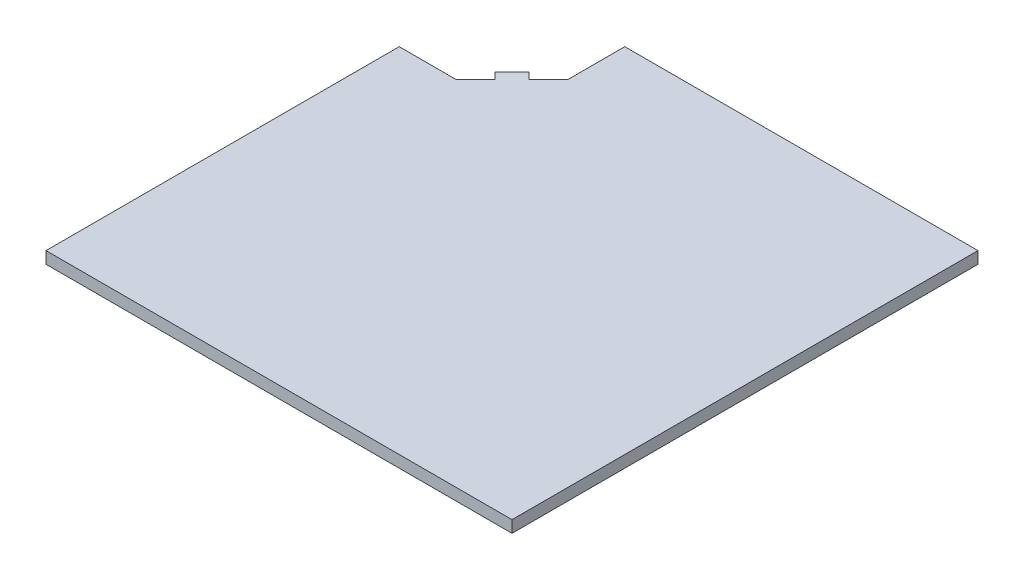
SolidWorks part; units mm, degrees
ref_plane "Front Plane" through (0, 0, 0) normal (0, 0, 1) x (1, 0, 0)
ref_plane "Top Plane" through (0, 0, 0) normal (0, 1, 0) x (1, 0, 0)
ref_plane "Right Plane" through (0, 0, 0) normal (1, 0, 0) x (0, 0, -1)
sketch "Sketch1" plane through (0, 0, 0) normal (0, 1, 0) x (1, 0, 0)
  line L1 (-3.925, -3.925) -> (3.925, -3.925)
  line L2 (-3.925, -3.925) -> (-3.925, 3.925)
  line L3 (-3.925, 3.925) -> (3.925, 3.925)
  line L4 (3.925, -3.925) -> (3.925, 3.925)
  line L5 (-3.925, -3.925) -> (3.925, 3.925) construction
  line L6 (-3.925, 3.925) -> (3.925, -3.925) construction
  point P0 (0, 0)
  dimension "D1" = 7.85
extrude "Boss-Extrude1" add sketch "Sketch1" along normal blind 0.2
sketch "Sketch3" plane through (0, 0.2, 0) normal (0, 1, 0) x (1, 0, 0)
  line L0 (-3.925, 2.025) -> (-2.973, 2.025)
  line L1 (-3.925, 3.925) -> (-3.925, -3.925) construction
  line L2 (-2.973, 2.025) -> (-2.6404, 2.3576)
  line L3 (-2.025, 2.973) -> (-2.025, 3.925)
  line L4 (3.925, 3.925) -> (-3.925, 3.925) construction
  line L5 (-2.025, 3.925) -> (-3.925, 3.925)
  line L6 (-3.925, 3.925) -> (-3.925, 2.025)
  line L7 (-3.925, -3.925) -> (3.925, -3.925) construction
  line L8 (-2.6404, 2.3576) -> (-2.7465, 2.4636)
  line L9 (-2.7465, 2.4636) -> (-2.4636, 2.7465)
  line L10 (-2.4636, 2.7465) -> (-2.3576, 2.6404)
  line L11 (-2.3576, 2.6404) -> (-2.025, 2.973)
  dimension "D1" = 5.95
  dimension "D2" = 0.4
  dimension "D3" = 0.15
  dimension "D4" = 0.3326
extrude "Cut-Extrude1" cut sketch "Sketch3" against normal through all
